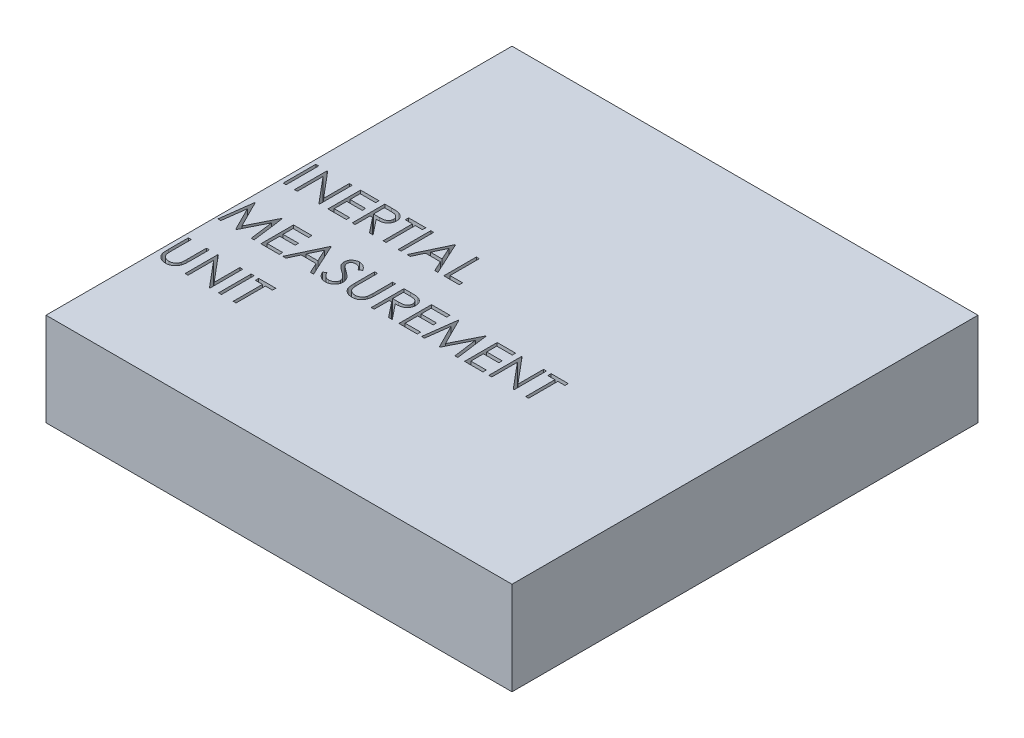
SolidWorks part; units mm, degrees
ref_plane "Front Plane" through (0, 0, 0) normal (0, 0, 1) x (1, 0, 0)
ref_plane "Top Plane" through (0, 0, 0) normal (0, 1, 0) x (1, 0, 0)
ref_plane "Right Plane" through (0, 0, 0) normal (1, 0, 0) x (0, 0, -1)
sketch "Sketch1" plane through (0, 0, 0) normal (0, 1, 0) x (1, 0, 0)
  line L1 (0, 0) -> (50, 0)
  line L2 (0, 0) -> (0, 50)
  line L3 (0, 50) -> (50, 50)
  line L4 (50, 0) -> (50, 50)
  dimension "D1" = 50
  dimension "D2" = 50
extrude "Boss-Extrude1" add sketch "Sketch1" along normal blind 10
sketch "Sketch2" plane through (0, 10, 0) normal (0, 1, 0) x (1, 0, 0)
  line L0 (0, 25) -> (50, 25) construction
  line L1 (0, 50) -> (0, 0) construction
  line L2 (50, 0) -> (50, 50) construction
  text T0 "INERTIAL\r\nMEASUREMENT\r\nUNIT"
extrude "Cut-Extrude1" cut sketch "Sketch2" against normal through all
